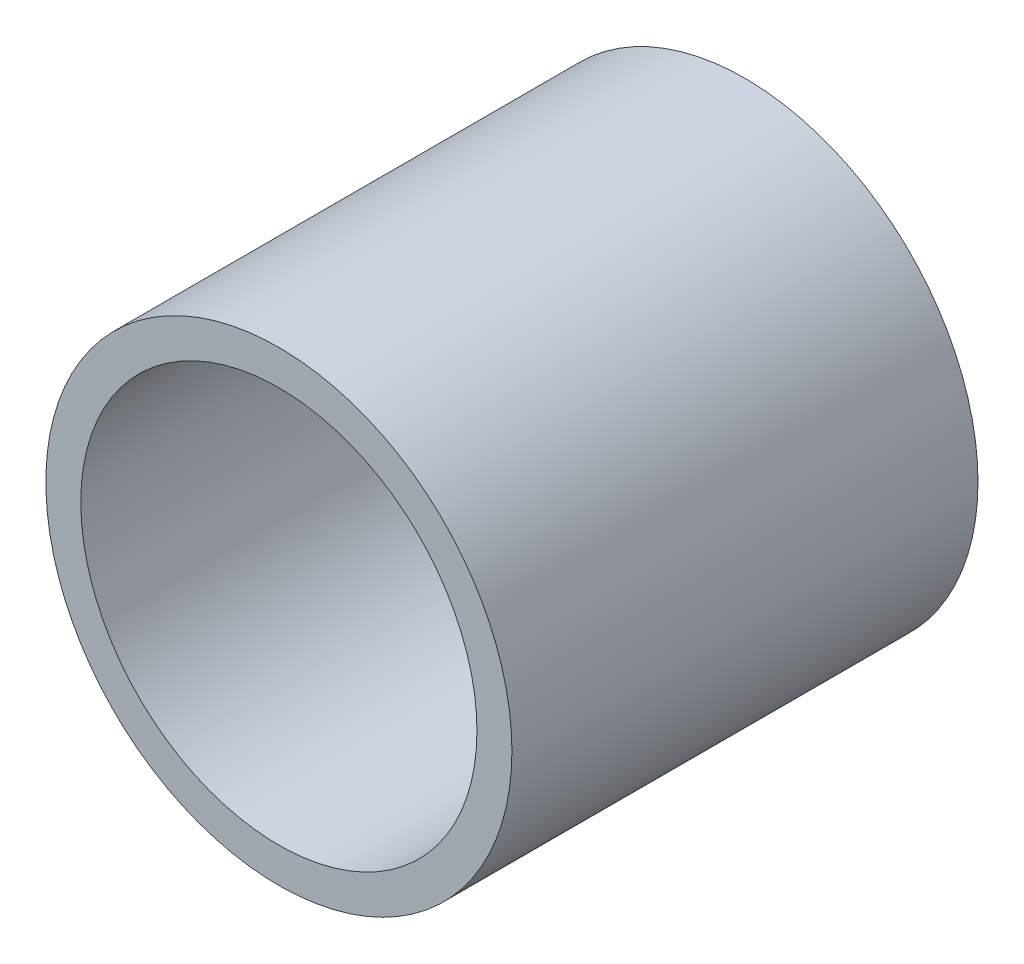
SolidWorks part; units mm, degrees
ref_plane "前视基准面" through (0, 0, 0) normal (0, 0, 1) x (1, 0, 0)
ref_plane "上视基准面" through (0, 0, 0) normal (0, 1, 0) x (1, 0, 0)
ref_plane "右视基准面" through (0, 0, 0) normal (1, 0, 0) x (0, 0, -1)
other "Configuration Table"
sketch "草图1" plane through (0, 0, 0) normal (0, 0, 1) x (1, 0, 0)
  circle A0 centre (-4.5248, 16.8873) radius 20
  dimension "D1" = 40
extrude "凸台-拉伸1" add sketch "草图1" along normal blind 40
sketch "草图2" plane through (0, 0, 40) normal (0, 0, 1) x (1, 0, 0)
  circle A0 centre (-4.5248, 16.8873) radius 17
  circle A1 centre (-4.5248, 16.8873) radius 20 construction
  dimension "D1" = 3
extrude "切除-拉伸1" cut sketch "草图2" against normal blind 37 contours A0
